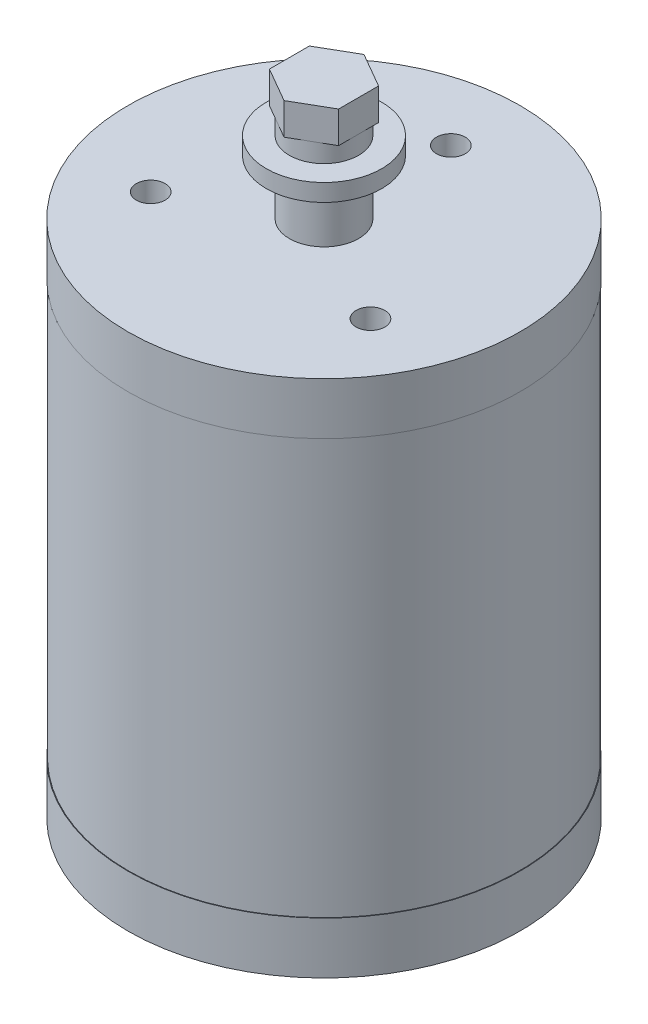
SolidWorks part; units mm, degrees
material "1060 Alloy"
ref_plane "Front Plane" through (0, 0, 0) normal (0, 0, 1) x (1, 0, 0)
ref_plane "Top Plane" through (0, 0, 0) normal (0, 1, 0) x (1, 0, 0)
ref_plane "Right Plane" through (0, 0, 0) normal (1, 0, 0) x (0, 0, -1)
sketch "Sketch1" plane through (0, 0, 0) normal (0, 1, 0) x (1, 0, 0)
  circle A0 centre (0, 0) radius 34
  dimension "D1" = 68
extrude "MainHousing" add sketch "Sketch1" along normal blind 90
sketch "Sketch2" plane through (0, 0, 0) normal (0, -1, 0) x (1, 0, 0)
  circle A0 centre (0, 0) radius 15
  dimension "D1" = 30
extrude "RearPart" add sketch "Sketch2" along normal blind 10
sketch "Sketch3" plane through (0, 90, 0) normal (0, 1, 0) x (1, 0, 0)
  circle A0 centre (0, 0) radius 6
  dimension "D1" = 12
extrude "Shaft" add sketch "Sketch3" along normal blind 9.5
sketch "Sketch4" plane through (0, 99.5, 0) normal (0, 1, 0) x (1, 0, 0)
  circle A0 centre (0, 0) radius 10
  dimension "D1" = 20
extrude "Gear" add sketch "Sketch4" along normal blind 3
sketch "Sketch5" plane through (0, 102.5, 0) normal (0, 1, 0) x (1, 0, 0)
  line L1 (0, 6.9282) -> (-6, 3.4641)
  line L2 (-6, 3.4641) -> (-6, -3.4641)
  line L3 (-6, -3.4641) -> (0, -6.9282)
  line L4 (0, -6.9282) -> (6, -3.4641)
  line L5 (6, -3.4641) -> (6, 3.4641)
  line L6 (6, 3.4641) -> (0, 6.9282)
  circle A0 centre (0, 0) radius 6 construction
  dimension "D1" = 12
extrude "HexBolt" add sketch "Sketch5" along normal blind 8.7
sketch "Sketch6" plane through (0, 102.5, 0) normal (0, 1, 0) x (1, 0, 0)
  line L0 (6, 3.4641) -> (0, 6.9282) construction
  circle A0 centre (0, 0) radius 6
  circle A1 centre (0, 0) radius 10
  circle A2 centre (0, 0) radius 10 construction
extrude "HexBoltCutout" cut sketch "Sketch6" along normal offset from surface (3.2 mm away) 5.5 up to face at (0, 111.2, 0)
sketch "Sketch7" plane through (0, 0, 0) normal (0, 1, 0) x (1, 0, 0)
  circle A0 centre (0, 0) radius 34
  circle A1 centre (0, 0) radius 33.9
  circle A2 centre (0, 0) radius 34 construction
  dimension "D1" = 0.1
extrude "Top/BottomSeperation" cut sketch "Sketch7" along normal offset from surface (72 mm away) 9 from offset 9 up to face at (0, 90, 6)
sketch "Sketch8" plane through (0, 90, 0) normal (0, 1, 0) x (1, 0, 0)
  circle A0 centre (0, 22) radius 2.5
  circle A1 centre (0, 0) radius 34 construction
  point P2 (0, 34)
  dimension "D2" = 5
  dimension "D1" = 12
extrude "ScrewHole" cut sketch "Sketch8" against normal blind 12.4
pattern_circular "ScrewHolePattern" count 3 over 360 about axis through (0, 0, 0) along (0, 1, 0) of "ScrewHole"
